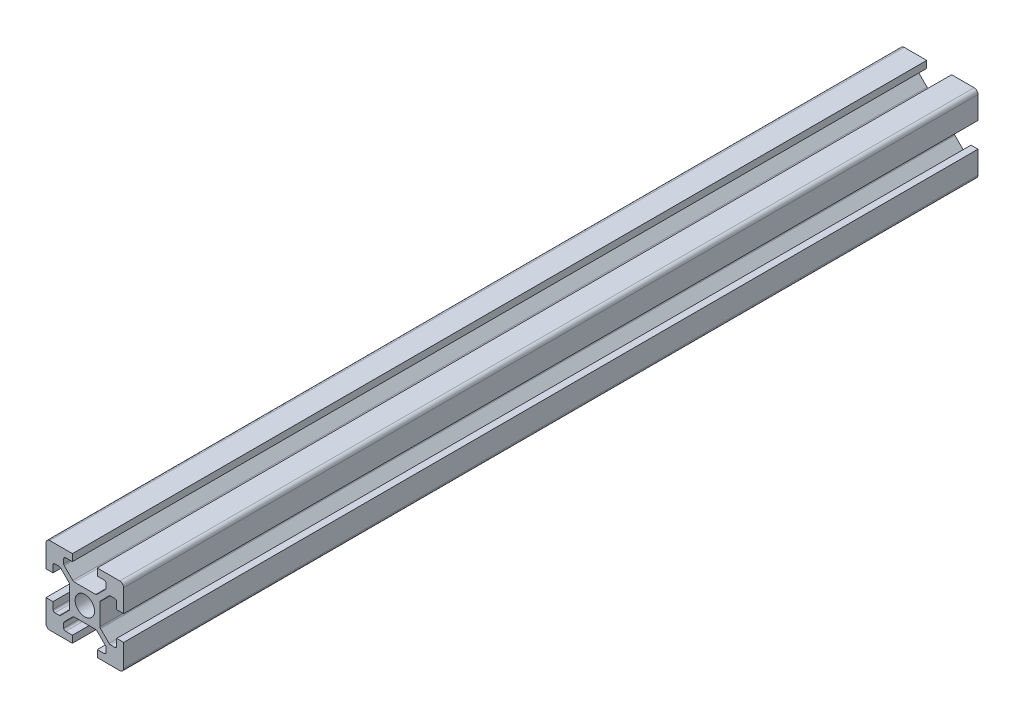
SolidWorks part; units mm, degrees
material "1060 Alloy"
ref_plane "Front Plane" through (0, 0, 0) normal (0, 0, 1) x (1, 0, 0)
ref_plane "Top Plane" through (0, 0, 0) normal (0, 1, 0) x (1, 0, 0)
ref_plane "Right Plane" through (0, 0, 0) normal (1, 0, 0) x (0, 0, -1)
sketch "Sketch1" plane through (0, 0, 0) normal (0, 0, 1) x (1, 0, 0)
  line L0 (20, 0) -> (-8.059, 28.059) construction
  line L1 (0, 0) -> (6.8, 0)
  line L2 (0, 0) -> (0, 6.8)
  line L3 (0, 20) -> (6.8, 20)
  line L4 (20, 0) -> (20, 6.8)
  line L5 (6.8, 20) -> (6.8, 18.2)
  line L6 (20, 20) -> (8.2322, 8.2322) construction
  line L7 (12.95, 6.1) -> (7.05, 6.1)
  line L8 (13.9, 7.05) -> (13.9, 12.95)
  line L9 (12.95, 13.9) -> (7.05, 13.9)
  line L10 (6.1, 7.05) -> (6.1, 12.95)
  line L11 (13.9, 6.1) -> (6.1, 13.9) construction
  line L12 (13.9, 13.9) -> (6.1, 6.1) construction
  line L13 (4.55, 16.4) -> (7.05, 13.9)
  line L14 (13.2, 18.2) -> (13.2, 20)
  line L15 (1.8, 6.8) -> (0, 6.8)
  line L16 (0, 13.2) -> (0, 20)
  line L17 (0, 13.2) -> (1.8, 13.2)
  line L18 (10, 10) -> (10, 13.9) construction
  line L19 (16.4, 4.55) -> (13.9, 7.05)
  line L20 (4.55, 16.4) -> (4.55, 18.2)
  line L21 (4.55, 18.2) -> (6.8, 18.2)
  line L22 (13.2, 18.2) -> (15.45, 18.2)
  line L23 (15.45, 18.2) -> (15.45, 16.4)
  line L24 (15.45, 16.4) -> (12.95, 13.9)
  line L25 (16.4, 4.55) -> (18.2, 4.55)
  line L26 (18.2, 4.55) -> (18.2, 6.8)
  line L27 (20, 6.8) -> (18.2, 6.8)
  line L28 (18.2, 13.2) -> (20, 13.2)
  line L29 (18.2, 13.2) -> (18.2, 15.45)
  line L30 (18.2, 15.45) -> (16.4, 15.45)
  line L31 (16.4, 15.45) -> (13.9, 12.95)
  line L32 (1.8, 4.55) -> (3.6, 4.55)
  line L33 (3.6, 15.45) -> (6.1, 12.95)
  line L34 (3.6, 15.45) -> (1.8, 15.45)
  line L35 (1.8, 15.45) -> (1.8, 13.2)
  line L36 (0, 13.2) -> (1.8, 13.2)
  line L37 (1.8, 6.8) -> (0, 6.8)
  line L38 (3.6, 4.55) -> (6.1, 7.05)
  line L39 (1.8, 6.8) -> (1.8, 4.55)
  line L40 (15.45, 3.6) -> (12.95, 6.1)
  line L41 (4.55, 3.6) -> (7.05, 6.1)
  line L42 (4.55, 1.8) -> (4.55, 3.6)
  line L43 (6.8, 1.8) -> (4.55, 1.8)
  line L44 (6.8, 1.8) -> (6.8, 0)
  line L45 (15.45, 3.6) -> (15.45, 1.8)
  line L46 (15.45, 1.8) -> (13.2, 1.8)
  line L47 (13.2, 0) -> (13.2, 1.8)
  line L48 (13.2, 20) -> (20, 20)
  line L49 (20, 13.2) -> (20, 20)
  line L50 (13.2, 0) -> (20, 0)
  line L51 (6.1, 6.1) -> (-5.5045, -5.5045) construction
  circle A0 centre (10, 10) radius 2.5
  point P25 (10, 16.4)
  point P39 (13.2, 19.1)
  point P46 (0.9, 6.8)
  dimension "D3" = 5
  dimension "D2" = 20
  dimension "D4" = 7.8
  dimension "D5" = 7.8
  dimension "D6" = 6.8
  dimension "D7" = 6.8
  dimension "D8" = 1.8
  dimension "D9" = 10.9
  dimension "D10" = 1.8
  dimension "D11" = 10.9
  dimension "D12" = 20
extrude "Boss-Extrude1" add sketch "Sketch1" along normal blind 220 contours L47 L50 L4 L27 L26 L25 L19 L8 L31 L30 L29 L28 L49 L48 L14 L22 L23 L24 L9 L13 L20 L21 L5 L3 L16 L17 L35 L34 L33 L10 L38 L32 L39 L15 L2 L1 L44 L43 L42 L41 L7 L40 L45 L46 A0
fillet "Fillet1" radius 1 4 edges at (20, 20, 110) (20, 0, 110) (0, 0, 110) (0, 20, 110)
fillet "Fillet2" radius 0.5 6 edges at (4.55, 18.2, 110) (4.55, 16.4, 110) (7.05, 13.9, 110) (15.45, 18.2, 110) (15.45, 16.4, 110) (12.95, 13.9, 110)
fillet "Fillet3" radius 0.5 6 edges at (18.2, 15.45, 110) (16.4, 15.45, 110) (13.9, 12.95, 110) (18.2, 4.55, 110) (13.9, 7.05, 110) (16.4, 4.55, 110)
fillet "Fillet4" radius 0.5 6 edges at (1.8, 15.45, 110) (3.6, 15.45, 110) (6.1, 12.95, 110) (3.6, 4.55, 110) (1.8, 4.55, 110) (6.1, 7.05, 110)
fillet "Fillet5" radius 0.5 6 edges at (7.05, 6.1, 110) (4.55, 3.6, 110) (4.55, 1.8, 110) (15.45, 1.8, 110) (15.45, 3.6, 110) (12.95, 6.1, 110)
